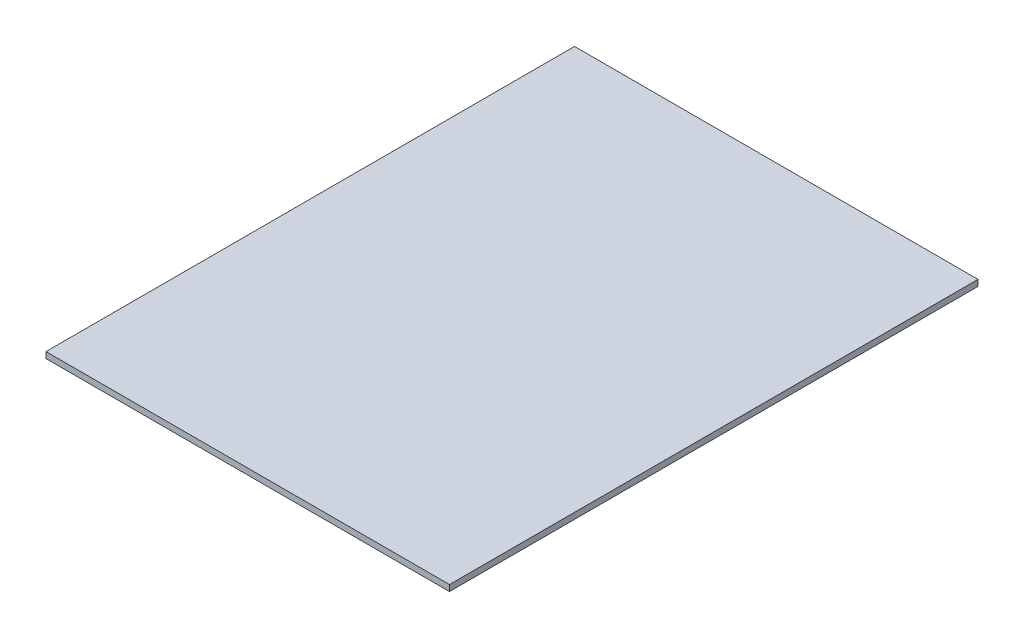
SolidWorks part; units mm, degrees
ref_plane "Front Plane" through (0, 0, 0) normal (0, 0, 1) x (1, 0, 0)
ref_plane "Top Plane" through (0, 0, 0) normal (0, 1, 0) x (1, 0, 0)
ref_plane "Right Plane" through (0, 0, 0) normal (1, 0, 0) x (0, 0, -1)
sketch "Sketch1" plane through (0, 0, 0) normal (0, 1, 0) x (1, 0, 0)
  line L1 (198.5, -260) -> (-198.5, -260)
  line L2 (198.5, -260) -> (198.5, 260)
  line L3 (198.5, 260) -> (-198.5, 260)
  line L4 (-198.5, -260) -> (-198.5, 260)
  line L5 (198.5, -260) -> (-198.5, 260) construction
  line L6 (198.5, 260) -> (-198.5, -260) construction
  point P0 (0, 0)
  dimension "D1" = 397
  dimension "D2" = 520
extrude "Boss-Extrude1" add sketch "Sketch1" along normal blind 6
